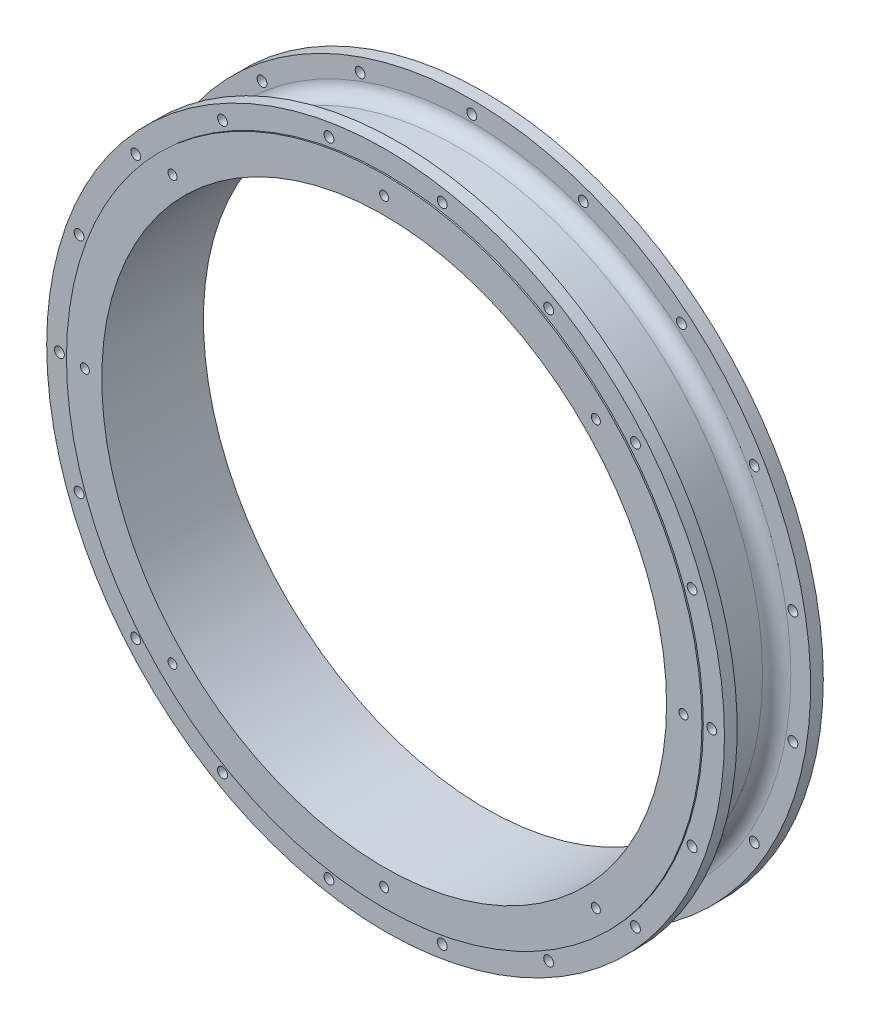
SolidWorks part; units mm, degrees
material "3.1305 (EN-AW 2117)"
ref_plane "Спереди" through (0, 0, 0) normal (0, 0, 1) x (1, 0, 0)
ref_plane "Сверху" through (0, 0, 0) normal (0, 1, 0) x (1, 0, 0)
ref_plane "Справа" through (0, 0, 0) normal (1, 0, 0) x (0, 0, -1)
sketch "Эскиз1" plane through (0, 0, 0) normal (0, 0, 1) x (1, 0, 0)
  circle A0 centre (0, 0) radius 120
extrude "Бобышка-Вытянуть1" add sketch "Эскиз1" along normal blind 35
sketch "Эскиз2" plane through (0, 0, 0) normal (0, 0, -1) x (-1, 0, 0)
  line L0 (0, 0) -> (-251.1474, 145) construction
  line L1 (0, 0) -> (-186.4084, 222.1529) construction
  line L2 (-186.4084, 222.1529) -> (-251.1474, 145) construction
  line L3 (0, 0) -> (-222.1529, 186.4084) construction
  circle A0 centre (0, 0) radius 115.5 construction
  circle A1 centre (0, 115.5) radius 1.75
  circle A2 centre (39.5033, 108.5345) radius 1.75
  circle A3 centre (74.242, 88.4781) radius 1.75
  circle A4 centre (100.0259, 57.75) radius 1.75
  circle A5 centre (113.7453, 20.0564) radius 1.75
  circle A6 centre (113.7453, -20.0564) radius 1.75
  circle A7 centre (100.0259, -57.75) radius 1.75
  circle A8 centre (74.242, -88.4781) radius 1.75
  circle A9 centre (39.5033, -108.5345) radius 1.75
  circle A10 centre (0, -115.5) radius 1.75
  circle A11 centre (-39.5033, -108.5345) radius 1.75
  circle A12 centre (-74.242, -88.4781) radius 1.75
  circle A13 centre (-100.0259, -57.75) radius 1.75
  circle A14 centre (-113.7453, -20.0564) radius 1.75
  circle A15 centre (-113.7453, 20.0564) radius 1.75
  circle A16 centre (-100.0259, 57.75) radius 1.75
  circle A17 centre (-74.242, 88.4781) radius 1.75
  circle A18 centre (-39.5033, 108.5345) radius 1.75
  point P42 (0, 0)
  dimension "D1" = 18
  dimension "D2" = 231
  dimension "D3" = 290
sketch "Эскиз4" plane through (0, 0, 35) normal (0, 0, 1) x (1, 0, 0)
  circle A0 centre (0, 0) radius 115.5 construction
  circle A1 centre (-115.5, 0) radius 1.75
  circle A2 centre (-108.5345, 39.5033) radius 1.75
  circle A3 centre (-88.4781, 74.242) radius 1.75
  circle A4 centre (-57.75, 100.0259) radius 1.75
  circle A5 centre (-20.0564, 113.7453) radius 1.75
  circle A6 centre (20.0564, 113.7453) radius 1.75
  circle A7 centre (57.75, 100.0259) radius 1.75
  circle A8 centre (88.4781, 74.242) radius 1.75
  circle A9 centre (108.5345, 39.5033) radius 1.75
  circle A10 centre (115.5, 0) radius 1.75
  circle A11 centre (108.5345, -39.5033) radius 1.75
  circle A12 centre (88.4781, -74.242) radius 1.75
  circle A13 centre (57.75, -100.0259) radius 1.75
  circle A14 centre (20.0564, -113.7453) radius 1.75
  circle A15 centre (-20.0564, -113.7453) radius 1.75
  circle A16 centre (-57.75, -100.0259) radius 1.75
  circle A17 centre (-88.4781, -74.242) radius 1.75
  circle A18 centre (-108.5345, -39.5033) radius 1.75
  point P42 (0, 0)
  dimension "D1" = 18
  dimension "D2" = 231
sketch "Эскиз5" plane through (0, 0, 35) normal (0, 0, 1) x (1, 0, 0)
  circle A0 centre (0, 0) radius 100
  dimension "D1" = 200
sketch "Эскиз6" plane through (0, 0, 0) normal (0, 0, -1) x (-1, 0, 0)
  circle A0 centre (0, 0) radius 112.5
sketch "Эскиз7" plane through (0, 0, 0) normal (0, 1, 0) x (1, 0, 0)
  line L0 (-120, 0) -> (-120, -4.5)
  line L1 (-120, 0) -> (-120, -35) construction
  line L2 (-120, -4.5) -> (-113, -4.5)
  line L3 (-108, -9.5) -> (-108, -25.5)
  line L4 (-113, -30.5) -> (-120, -30.5)
  line L5 (-120, -30.5) -> (-120, -35)
  line L6 (-120, -35) -> (-128.2207, -35)
  line L7 (-128.2207, -35) -> (-128.2207, 0)
  line L8 (-128.2207, 0) -> (-120, 0)
  arc A0 (-108, -25.5) -> (-113, -30.5) centre (-113, -25.5) cw
  arc A1 (-113, -4.5) -> (-108, -9.5) centre (-113, -9.5) cw
  dimension "D1" = 5
  dimension "D2" = 12
sketch "Эскиз8" plane through (0, 0, 0) normal (0, 1, 0) x (1, 0, 0)
  line L0 (0, 0) -> (0, -35)
revolve "Вырез-Повернуть2" cut sketch "Эскиз7" angle 360 about L0
sketch "Эскиз9" plane through (0, 0, 35) normal (0, 0, 1) x (1, 0, 0)
  circle A0 centre (0, 0) radius 112.5
extrude "Бобышка-Вытянуть2" add sketch "Эскиз9" along normal blind 0.5
extrude "Бобышка-Вытянуть3" add sketch "Эскиз6" along normal blind 0.5 contours A0
extrude "Вырез-Вытянуть2" cut sketch "Эскиз5" against normal through all both and the other way through all contours A0
extrude "Вырез-Вытянуть3" cut sketch "Эскиз4" against normal blind 5 contours A18
extrude "Вырез-Вытянуть4" cut sketch "Эскиз2" against normal blind 5
sketch "Эскиз10" plane through (0, 0, -0.5) normal (0, 0, -1) x (-1, 0, 0)
  circle A0 centre (0, 0) radius 106 construction
  circle A1 centre (0, 106) radius 1.6
  circle A2 centre (74.9533, 74.9533) radius 1.6
  circle A3 centre (106, 0) radius 1.6
  circle A4 centre (74.9533, -74.9533) radius 1.6
  circle A5 centre (0, -106) radius 1.6
  circle A6 centre (-74.9533, -74.9533) radius 1.6
  circle A7 centre (-106, 0) radius 1.6
  circle A8 centre (-74.9533, 74.9533) radius 1.6
  point P21 (0, 0)
  dimension "D1" = 212
  dimension "D2" = 8
  dimension "D3" = 3.2
extrude "Вырез-Вытянуть6" cut sketch "Эскиз10" against normal blind 6
sketch "Эскиз11" plane through (0, 0, 0) normal (0, 0, 1) x (1, 0, 0)
  circle A0 centre (0, 0) radius 106 construction
  circle A1 centre (0, 106) radius 1.6
  circle A2 centre (74.9533, 74.9533) radius 1.6
  circle A3 centre (106, 0) radius 1.6
  circle A4 centre (74.9533, -74.9533) radius 1.6
  circle A5 centre (0, -106) radius 1.6
  circle A6 centre (-74.9533, -74.9533) radius 1.6
  circle A7 centre (-106, 0) radius 1.6
  circle A8 centre (-74.9533, 74.9533) radius 1.6
  point P21 (0, 0)
  dimension "D1" = 212
  dimension "D2" = 8
  dimension "D3" = 3.2
extrude "Вырез-Вытянуть7" cut sketch "Эскиз11" against normal blind 6.5 from offset 36
sketch3d "Трехмерный эскиз1"
  line L0 (-20.0564, 113.7453, 35) -> (-20.0564, 113.7453, 30.5)
  line L1 (-20.0564, 113.7453, 30.5) -> (-20.0564, 113.7453, 35) construction
  line L2 (-57.75, 100.0259, 35) -> (-57.75, 100.0259, 30.5)
  line L3 (-57.75, 100.0259, 30.5) -> (-57.75, 100.0259, 35) construction
  line L4 (20.0564, 113.7453, 35) -> (20.0564, 113.7453, 30.5)
  line L5 (20.0564, 113.7453, 30.5) -> (20.0564, 113.7453, 35) construction
  line L6 (57.75, 100.0259, 35) -> (57.75, 100.0259, 30.5)
  line L7 (57.75, 100.0259, 30.5) -> (57.75, 100.0259, 35) construction
  line L8 (88.4781, 74.242, 35) -> (88.4781, 74.242, 30.5)
  line L9 (88.4781, 74.242, 30.5) -> (88.4781, 74.242, 35) construction
  line L10 (108.5345, 39.5033, 35) -> (108.5345, 39.5033, 30.5)
  line L11 (108.5345, 39.5033, 30.5) -> (108.5345, 39.5033, 35) construction
  line L12 (115.5, 0, 35) -> (115.5, 0, 30.5)
  line L13 (115.5, 0, 30.5) -> (115.5, 0, 35) construction
  line L14 (108.5345, -39.5033, 35) -> (108.5345, -39.5033, 30.5)
  line L15 (108.5345, -39.5033, 30.5) -> (108.5345, -39.5033, 35) construction
  line L16 (88.4781, -74.242, 35) -> (88.4781, -74.242, 30.5)
  line L17 (88.4781, -74.242, 30.5) -> (88.4781, -74.242, 35) construction
  line L18 (57.75, -100.0259, 35) -> (57.75, -100.0259, 30.5)
  line L19 (57.75, -100.0259, 30.5) -> (57.75, -100.0259, 35) construction
  line L20 (20.0564, -113.7453, 35) -> (20.0564, -113.7453, 30.5)
  line L21 (20.0564, -113.7453, 30.5) -> (20.0564, -113.7453, 35) construction
  line L22 (-57.75, -100.0259, 35) -> (-57.75, -100.0259, 30.5)
  line L23 (-57.75, -100.0259, 30.5) -> (-57.75, -100.0259, 35) construction
  line L24 (-20.0564, -113.7453, 35) -> (-20.0564, -113.7453, 30.5)
  line L25 (-20.0564, -113.7453, 30.5) -> (-20.0564, -113.7453, 35) construction
  line L26 (-88.4781, -74.242, 35) -> (-88.4781, -74.242, 30.5)
  line L27 (-88.4781, -74.242, 30.5) -> (-88.4781, -74.242, 35) construction
  line L28 (-108.5345, -39.5033, 35) -> (-108.5345, -39.5033, 30.5)
  line L29 (-108.5345, -39.5033, 30.5) -> (-108.5345, -39.5033, 35) construction
  line L30 (-115.5, 0, 35) -> (-115.5, 0, 30.5)
  line L31 (-115.5, 0, 30.5) -> (-115.5, 0, 35) construction
  line L32 (-108.5345, 39.5033, 35) -> (-108.5345, 39.5033, 30.5)
  line L33 (-108.5345, 39.5033, 30.5) -> (-108.5345, 39.5033, 35) construction
  line L34 (-88.4781, 74.242, 35) -> (-88.4781, 74.242, 30.5)
  line L35 (-88.4781, 74.242, 30.5) -> (-88.4781, 74.242, 35) construction
  circle A0 centre (0, 0, 35) radius 115.5 construction
  point P29 (0, 0, 150.5)
sketch "Эскиз12" plane through (0, 0, 4.5) normal (0, 0, 1) x (1, 0, 0)
  circle A0 centre (0, 0) radius 115.5 construction
  circle A1 centre (0, 115.5) radius 1.75
  circle A2 centre (39.5033, 108.5345) radius 1.75
  circle A3 centre (74.242, 88.4781) radius 1.75
  circle A4 centre (100.0259, 57.75) radius 1.75
  circle A5 centre (113.7453, 20.0564) radius 1.75
  circle A6 centre (113.7453, -20.0564) radius 1.75
  circle A7 centre (100.0259, -57.75) radius 1.75
  circle A8 centre (74.242, -88.4781) radius 1.75
  circle A9 centre (39.5033, -108.5345) radius 1.75
  circle A10 centre (0, -115.5) radius 1.75
  circle A11 centre (-39.5033, -108.5345) radius 1.75
  circle A12 centre (-74.242, -88.4781) radius 1.75
  circle A13 centre (-100.0259, -57.75) radius 1.75
  circle A14 centre (-113.7453, -20.0564) radius 1.75
  circle A15 centre (-113.7453, 20.0564) radius 1.75
  circle A16 centre (-100.0259, 57.75) radius 1.75
  circle A17 centre (-74.242, 88.4781) radius 1.75
  circle A18 centre (-39.5033, 108.5345) radius 1.75
  point P42 (0, 0)
  dimension "D1" = 18
  dimension "D2" = 231
sketch "Эскиз14" plane through (0, 0, 30.5) normal (0, 0, 1) x (1, 0, 0)
  circle A0 centre (0, 0) radius 115.5 construction
  circle A1 centre (-115.5, 0) radius 1.75
  circle A2 centre (-108.5345, 39.5033) radius 1.75
  circle A3 centre (-88.4781, 74.242) radius 1.75
  circle A4 centre (-57.75, 100.0259) radius 1.75
  circle A5 centre (-20.0564, 113.7453) radius 1.75
  circle A6 centre (20.0564, 113.7453) radius 1.75
  circle A7 centre (57.75, 100.0259) radius 1.75
  circle A8 centre (88.4781, 74.242) radius 1.75
  circle A9 centre (108.5345, 39.5033) radius 1.75
  circle A10 centre (115.5, 0) radius 1.75
  circle A11 centre (108.5345, -39.5033) radius 1.75
  circle A12 centre (88.4781, -74.242) radius 1.75
  circle A13 centre (57.75, -100.0259) radius 1.75
  circle A14 centre (20.0564, -113.7453) radius 1.75
  circle A15 centre (-20.0564, -113.7453) radius 1.75
  circle A16 centre (-57.75, -100.0259) radius 1.75
  circle A17 centre (-88.4781, -74.242) radius 1.75
  circle A18 centre (-108.5345, -39.5033) radius 1.75
  point P42 (0, 0)
  dimension "D1" = 18
  dimension "D2" = 231
